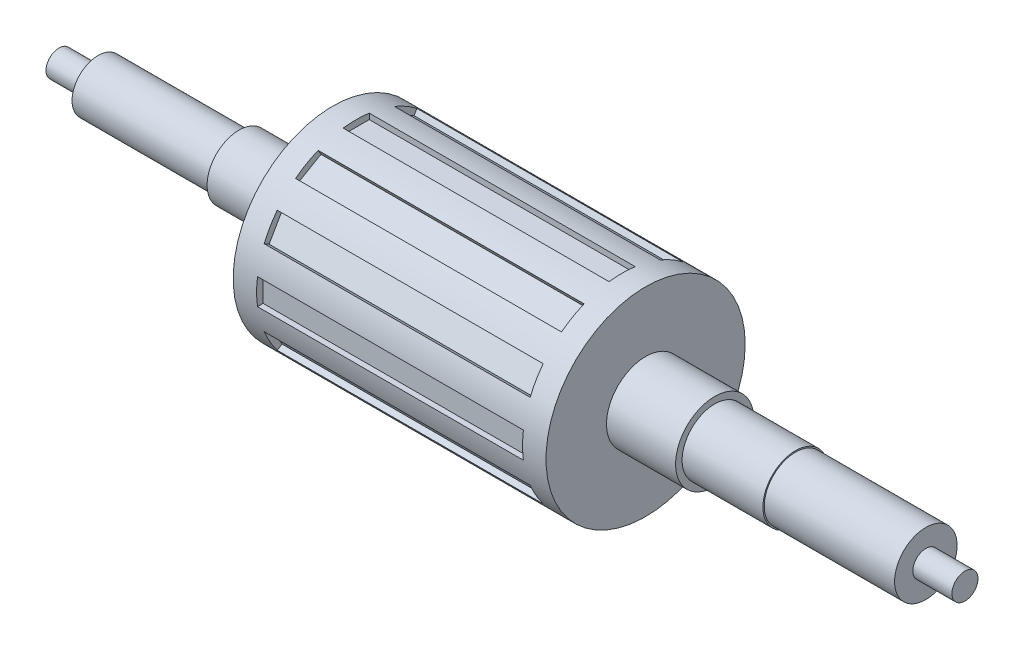
SolidWorks part; units mm, degrees
ref_plane "Front Plane" through (0, 0, 0) normal (0, 0, 1) x (1, 0, 0)
ref_plane "Top Plane" through (0, 0, 0) normal (0, 1, 0) x (1, 0, 0)
ref_plane "Right Plane" through (0, 0, 0) normal (1, 0, 0) x (0, 0, -1)
sketch "Sketch1" plane through (0, 0, 0) normal (0, 0, 1) x (1, 0, 0)
  line L0 (0, 0) -> (0, 5)
  line L1 (0, 5) -> (15, 5)
  line L2 (15, 5) -> (15, 10)
  line L3 (15, 10) -> (69, 10)
  line L4 (69, 10) -> (69, 12.2)
  line L5 (69, 12.2) -> (105, 12.2)
  line L6 (105, 12.2) -> (105, 38.2)
  line L7 (105, 38.2) -> (225, 38.2)
  line L8 (225, 38.2) -> (225, 15)
  line L9 (225, 15) -> (251.5, 15)
  line L10 (251.5, 15) -> (251.5, 12.5)
  line L11 (251.5, 12.5) -> (282.5, 12.5)
  line L12 (282.5, 12.5) -> (282.5, 12)
  line L13 (282.5, 12) -> (332.5, 12)
  line L14 (332.5, 12) -> (332.5, 5)
  line L15 (332.5, 5) -> (347.5, 5)
  line L16 (347.5, 5) -> (347.5, 0)
  line L17 (347.5, 0) -> (0, 0) construction
  line L18 (0, 0) -> (347.5, 0)
  dimension "D1" = 5
  dimension "D2" = 15
  dimension "D3" = 54
  dimension "D4" = 10
  dimension "D5" = 12.2
  dimension "D6" = 38.2
  dimension "D7" = 36
  dimension "D8" = 120
  dimension "D9" = 26.5
  dimension "D10" = 2.5
  dimension "D11" = 31
  dimension "D12" = 0.5
  dimension "D13" = 50
  dimension "D14" = 7
  dimension "D15" = 15
  dimension "D17" = 15
revolve "Revolve1" add sketch "Sketch1" angle 360 about L17
ref_plane "Plane1" through (216, 0, 0) normal (1, 0, 0) x (0, 0, -1)
sketch "Sketch2" plane through (216, 0, 0) normal (1, 0, 0) x (0, 0, -1)
  line L1 (38.2, 0) -> (38.2, 5)
  line L2 (38.2, 5) -> (35.7, 5)
  line L3 (35.7, 5) -> (35.7, -5)
  line L4 (35.7, -5) -> (38.2, -5)
  line L5 (38.2, -5) -> (38.2, 0)
  dimension "D1" = 2.5
  dimension "D2" = 10
  dimension "D3" = 5
extrude "Cut-Extrude2" cut sketch "Sketch2" against normal blind 102
pattern_circular "CirPattern2" count 12 over 360 about axis through (0, 0, 0) along (1, 0, 0) of "Cut-Extrude2"
